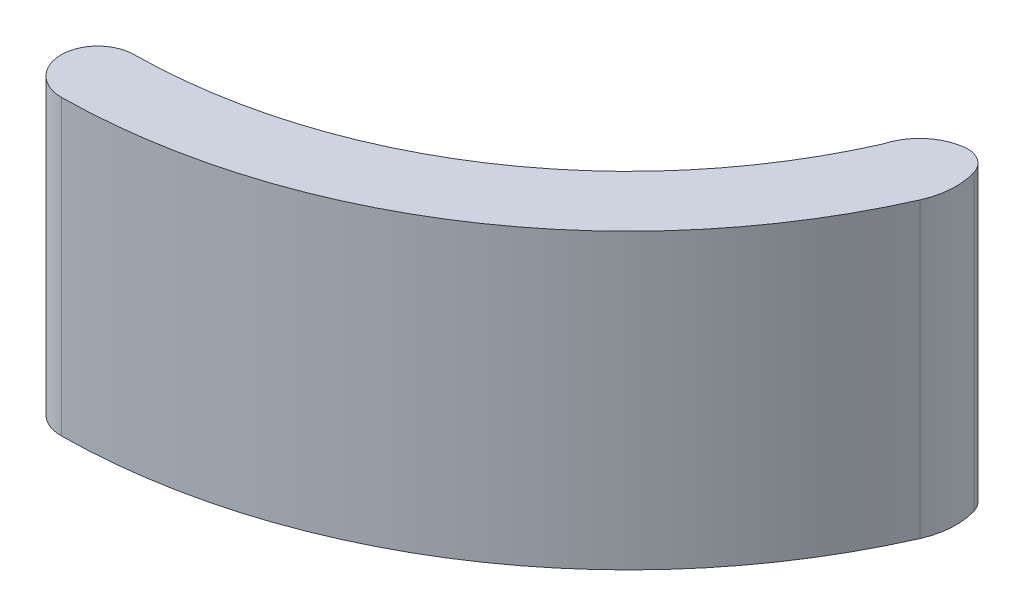
SolidWorks part; units mm, degrees
ref_plane "Front Plane" through (0, 0, 0) normal (0, 0, 1) x (1, 0, 0)
ref_plane "Top Plane" through (0, 0, 0) normal (0, 1, 0) x (1, 0, 0)
ref_plane "Right Plane" through (0, 0, 0) normal (1, 0, 0) x (0, 0, -1)
sketch "Sketch2" plane through (0, 0, 0) normal (0, 1, 0) x (1, 0, 0)
  arc A0 (64.0089, 11.1433) -> (63.7191, 16.5731) centre (58.5229, 13.5731) ccw
  arc A1 (21.613, -16.7175) -> (64.0089, 11.1433) centre (21.1951, 30.1058) ccw
  arc A5 (21.5595, -10.7177) -> (58.5229, 13.5731) centre (21.1951, 30.1058) ccw
  arc A6 (21.5595, -10.7177) -> (21.613, -16.7175) centre (21.5862, -13.7176) ccw
  arc A7 (63.7191, 16.5731) -> (58.5229, 13.5731) centre (62.621, 12.475) ccw
extrude "Boss-Extrude2" add sketch "Sketch2" along normal blind 24
fillet "Fillet3" radius 2 1 edges at (63.7191, 12, -16.5731)
